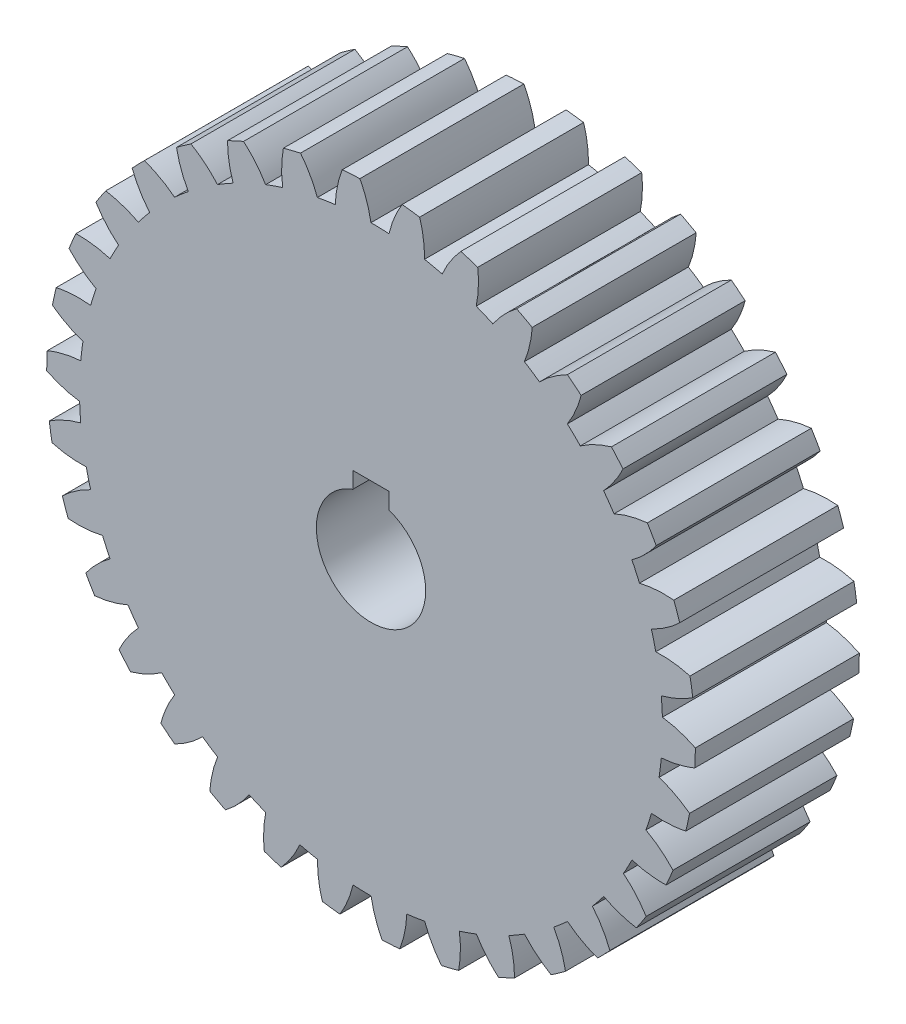
SolidWorks part; units mm, degrees
ref_plane "Front Plane" through (0, 0, 0) normal (0, 0, 1) x (1, 0, 0)
ref_plane "Top Plane" through (0, 0, 0) normal (0, 1, 0) x (1, 0, 0)
ref_plane "Right Plane" through (0, 0, 0) normal (1, 0, 0) x (0, 0, -1)
sketch "Sketch1" plane through (0, 0, 0) normal (0, 0, 1) x (1, 0, 0)
  line L0 (0, 0) -> (0, 31.945) construction
  line L1 (0, 0) -> (-6.9142, 31.1878) construction
  line L2 (0, 0) -> (-13.5005, 28.952) construction
  line L3 (0, 0) -> (-19.4469, 25.3437) construction
  line L4 (0, 0) -> (-24.4713, 20.5339) construction
  line L5 (-6.9142, 31.1878) -> (-0.1094, 32.6964) construction
  line L6 (-13.5005, 28.952) -> (-0.8666, 34.8433) construction
  line L7 (-19.4469, 25.3437) -> (-2.8579, 38.0729) construction
  line L8 (-24.4713, 20.5339) -> (-6.5504, 41.8912) construction
  line L9 (-0.5242, 33.996) -> (-3.6598, 33.8025) construction
  line L10 (-2.092, 33.8992) -> (0, 0) construction
  circle A0 centre (0, 0) radius 31.945 construction
  circle A1 centre (0, 0) radius 34 construction
  arc A2 (-1.2244, 35.5789) -> (-3.1595, 35.4595) centre (0, 0) ccw
  circle A3 centre (0, 0) radius 32
  spline S0 degree 3 poles (-0.0085, 32) (-0.1653, 32.9957) (-0.5453, 34.2042) (-1.0976, 35.3372) (-1.2244, 35.5789) knots 0.004504 0.004504 0.004504 0.004504 0.249371 0.316995 0.316995 0.316995 0.316995
  spline S1 degree 3 poles (-3.9261, 31.7582) (-3.893, 32.7657) (-3.6645, 34.0117) (-3.2557, 35.204) (-3.1595, 35.4595) knots 0.004504 0.004504 0.004504 0.004504 0.249371 0.316995 0.316995 0.316995 0.316995
  point P11 (0, 0)
  dimension "D3" = 63.89
  dimension "D8" = 68
  dimension "D10" = 71.2
  dimension "D11" = 64
  dimension "D2" = 50
  dimension "D4" = 6.97
  dimension "D5" = 13.94
  dimension "D6" = 20.91
  dimension "D7" = 27.88
  dimension "D9" = 3.1416
  dimension "D1" = 5
sketch "Sketch2" plane through (0, 0, 0) normal (0, 0, 1) x (1, 0, 0)
  circle A0 centre (0, 0) radius 32
  dimension "D1" = 64
extrude "Boss-Extrude1" add sketch "Sketch2" along normal blind 18
sketch "Sketch3" plane through (0, 0, 18) normal (0, 0, 1) x (1, 0, 0)
  circle A0 centre (0, 0) radius 32 construction
  arc A1 (-1.2244, 35.5789) -> (-3.1595, 35.4595) centre (0, 0) ccw construction
  arc A2 (-0.0085, 32) -> (-3.9261, 31.7582) centre (0, 0) ccw
  arc A3 (-1.2244, 35.5789) -> (-3.1595, 35.4595) centre (0, 0) ccw
  arc A4 (5.334, 35.1981) -> (3.41, 35.4363) centre (0, 0) ccw
  arc A5 (5.8716, 31.4567) -> (1.9763, 31.9389) centre (0, 0) ccw
  arc A6 (11.7108, 33.6187) -> (9.8633, 34.2064) centre (0, 0) ccw
  arc A7 (11.5518, 29.8422) -> (7.8114, 31.032) centre (0, 0) ccw
  arc A8 (17.6889, 30.8944) -> (15.9808, 31.8115) centre (0, 0) ccw
  arc A9 (16.8386, 27.2114) -> (13.3805, 29.0682) centre (0, 0) ccw
  arc A10 (23.0645, 27.1181) -> (21.554, 28.3334) centre (0, 0) ccw
  arc A11 (21.552, 23.654) -> (18.4939, 26.1146) centre (0, 0) ccw
  arc A12 (27.6547, 22.4182) -> (26.3933, 23.8905) centre (0, 0) ccw
  arc A13 (25.5314, 19.2911) -> (22.9776, 22.2717) centre (0, 0) ccw
  arc A14 (31.3032, 16.955) -> (30.3338, 18.6339) centre (0, 0) ccw
  arc A15 (28.6414, 14.2712) -> (26.6788, 17.6704) centre (0, 0) ccw
  arc A16 (33.8856, 10.9143) -> (33.2412, 12.7428) centre (0, 0) ccw
  arc A17 (30.7761, 8.7654) -> (29.4714, 12.4673) centre (0, 0) ccw
  arc A18 (35.3142, 4.502) -> (35.0167, 6.4178) centre (0, 0) ccw
  arc A19 (31.8627, 2.9611) -> (31.2605, 6.8397) centre (0, 0) ccw
  arc A20 (35.5401, -2.0636) -> (35.5998, -0.1258) centre (0, 0) ccw
  arc A21 (31.8643, -2.9441) -> (31.985, 0.9791) centre (0, 0) ccw
  arc A22 (34.5558, -8.5589) -> (34.9705, -6.6651) centre (0, 0) ccw
  arc A23 (30.7807, -8.749) -> (31.6203, -4.9148) centre (0, 0) ccw
  arc A24 (32.3947, -14.7628) -> (33.1504, -12.9774) centre (0, 0) ccw
  arc A25 (28.649, -14.256) -> (30.1788, -10.6413) centre (0, 0) ccw
  arc A26 (29.1305, -20.464) -> (30.2013, -18.8478) centre (0, 0) ccw
  arc A27 (25.5417, -19.2775) -> (27.7096, -16.0055) centre (0, 0) ccw
  arc A28 (24.8742, -25.4682) -> (26.2238, -24.0764) centre (0, 0) ccw
  arc A29 (21.5645, -23.6426) -> (24.2968, -20.8246) centre (0, 0) ccw
  arc A30 (19.7709, -29.6052) -> (21.3533, -28.485) centre (0, 0) ccw
  arc A31 (16.8531, -27.2025) -> (20.0566, -24.9345) centre (0, 0) ccw
  arc A32 (13.9944, -32.7341) -> (15.7556, -31.9237) centre (0, 0) ccw
  arc A33 (11.5677, -29.836) -> (15.1334, -28.1954) centre (0, 0) ccw
  arc A34 (7.7412, -34.7481) -> (9.6214, -34.2752) centre (0, 0) ccw
  arc A35 (5.8883, -31.4536) -> (9.6949, -30.4961) centre (0, 0) ccw
  arc A36 (1.2244, -35.5789) -> (3.1595, -35.4595) centre (0, 0) ccw
  arc A37 (0.0085, -32) -> (3.9261, -31.7582) centre (0, 0) ccw
  arc A38 (-5.334, -35.1981) -> (-3.41, -35.4363) centre (0, 0) ccw
  arc A39 (-5.8716, -31.4567) -> (-1.9763, -31.9389) centre (0, 0) ccw
  arc A40 (-11.7108, -33.6187) -> (-9.8633, -34.2064) centre (0, 0) ccw
  arc A41 (-11.5518, -29.8422) -> (-7.8114, -31.032) centre (0, 0) ccw
  arc A42 (-17.6889, -30.8944) -> (-15.9808, -31.8115) centre (0, 0) ccw
  arc A43 (-16.8386, -27.2114) -> (-13.3805, -29.0682) centre (0, 0) ccw
  arc A44 (-23.0645, -27.1181) -> (-21.554, -28.3334) centre (0, 0) ccw
  arc A45 (-21.552, -23.654) -> (-18.4939, -26.1146) centre (0, 0) ccw
  arc A46 (-27.6547, -22.4182) -> (-26.3933, -23.8905) centre (0, 0) ccw
  arc A47 (-25.5314, -19.2911) -> (-22.9776, -22.2717) centre (0, 0) ccw
  arc A48 (-31.3032, -16.955) -> (-30.3338, -18.6339) centre (0, 0) ccw
  arc A49 (-28.6414, -14.2712) -> (-26.6788, -17.6704) centre (0, 0) ccw
  arc A50 (-33.8856, -10.9143) -> (-33.2412, -12.7428) centre (0, 0) ccw
  arc A51 (-30.7761, -8.7654) -> (-29.4714, -12.4673) centre (0, 0) ccw
  arc A52 (-35.3142, -4.502) -> (-35.0167, -6.4178) centre (0, 0) ccw
  arc A53 (-31.8627, -2.9611) -> (-31.2605, -6.8397) centre (0, 0) ccw
  arc A54 (-35.5401, 2.0636) -> (-35.5998, 0.1258) centre (0, 0) ccw
  arc A55 (-31.8643, 2.9441) -> (-31.985, -0.9791) centre (0, 0) ccw
  arc A56 (-34.5558, 8.5589) -> (-34.9705, 6.6651) centre (0, 0) ccw
  arc A57 (-30.7807, 8.749) -> (-31.6203, 4.9148) centre (0, 0) ccw
  arc A58 (-32.3947, 14.7628) -> (-33.1504, 12.9774) centre (0, 0) ccw
  arc A59 (-28.649, 14.256) -> (-30.1788, 10.6413) centre (0, 0) ccw
  arc A60 (-29.1305, 20.464) -> (-30.2013, 18.8478) centre (0, 0) ccw
  arc A61 (-25.5417, 19.2775) -> (-27.7096, 16.0055) centre (0, 0) ccw
  arc A62 (-24.8742, 25.4682) -> (-26.2238, 24.0764) centre (0, 0) ccw
  arc A63 (-21.5645, 23.6426) -> (-24.2968, 20.8246) centre (0, 0) ccw
  arc A64 (-19.7709, 29.6052) -> (-21.3533, 28.485) centre (0, 0) ccw
  arc A65 (-16.8531, 27.2025) -> (-20.0566, 24.9345) centre (0, 0) ccw
  arc A66 (-13.9944, 32.7341) -> (-15.7556, 31.9237) centre (0, 0) ccw
  arc A67 (-11.5677, 29.836) -> (-15.1334, 28.1954) centre (0, 0) ccw
  arc A68 (-7.7412, 34.7481) -> (-9.6214, 34.2752) centre (0, 0) ccw
  arc A69 (-5.8883, 31.4536) -> (-9.6949, 30.4961) centre (0, 0) ccw
  spline S0 degree 3 poles (-2952.0058, -485.1321) (-147.5375, -118.176) (204.0978, 131.3339) (-278.5397, 15.7851) (2997.7022, 113.4453) knots -9.84774 -9.84774 -9.84774 -9.84774 0.249371 11.892847 11.892847 11.892847 11.892847 only from (-0.0085, 32) to (-1.2244, 35.5789) construction
  spline S1 degree 3 poles (2989.2564, -118.4971) (160.9487, -99.1389) (-218.6978, 105.2425) (274.4857, 49.9132) (-2988.9027, -255.9828) knots -9.847748 -9.847748 -9.847748 -9.847748 0.249371 11.892857 11.892857 11.892857 11.892857 only from (-3.9261, 31.7582) to (-3.1595, 35.4595) construction
  spline S2 degree 3 poles (-0.0085, 32) (-0.1653, 32.9957) (-0.5453, 34.2042) (-1.0976, 35.3372) (-1.2244, 35.5789) knots 0.004504 0.004504 0.004504 0.004504 0.249371 0.316995 0.316995 0.316995 0.316995
  spline S3 degree 3 poles (-3.9261, 31.7582) (-3.893, 32.7657) (-3.6645, 34.0117) (-3.2557, 35.204) (-3.1595, 35.4595) knots 0.004504 0.004504 0.004504 0.004504 0.249371 0.316995 0.316995 0.316995 0.316995
  spline S4 degree 3 poles (1.9763, 31.9389) (2.194, 32.9231) (2.6475, 34.1059) (3.2685, 35.2029) (3.41, 35.4363) knots 0.004504 0.004504 0.004504 0.004504 0.249371 0.316995 0.316995 0.316995 0.316995
  spline S5 degree 3 poles (5.8716, 31.4567) (5.9005, 32.4643) (5.749, 33.722) (5.4143, 34.9372) (5.334, 35.1981) knots 0.004504 0.004504 0.004504 0.004504 0.249371 0.316995 0.316995 0.316995 0.316995
  spline S6 degree 3 poles (7.8114, 31.032) (8.2062, 31.9594) (8.8694, 33.0387) (9.6814, 34.0029) (9.8633, 34.2064) knots 0.004504 0.004504 0.004504 0.004504 0.249371 0.316995 0.316995 0.316995 0.316995
  spline S7 degree 3 poles (11.5518, 29.8422) (11.7653, 30.8273) (11.8475, 32.0914) (11.7418, 33.3475) (11.7108, 33.6187) knots 0.004504 0.004504 0.004504 0.004504 0.249371 0.316995 0.316995 0.316995 0.316995
  spline S8 degree 3 poles (13.3805, 29.0682) (13.939, 29.9073) (14.7892, 30.8464) (15.7645, 31.645) (15.9808, 31.8115) knots 0.004504 0.004504 0.004504 0.004504 0.249371 0.316995 0.316995 0.316995 0.316995
  spline S9 degree 3 poles (16.8386, 27.2114) (17.2295, 28.1405) (17.5426, 29.368) (17.6695, 30.6221) (17.6889, 30.8944) knots 0.004504 0.004504 0.004504 0.004504 0.249371 0.316995 0.316995 0.316995 0.316995
  spline S10 degree 3 poles (18.4939, 26.1146) (19.1972, 26.8368) (20.2054, 27.6037) (21.3108, 28.2094) (21.554, 28.3334) knots 0.004504 0.004504 0.004504 0.004504 0.249371 0.316995 0.316995 0.316995 0.316995
  spline S11 degree 3 poles (21.552, 23.654) (22.1069, 24.4955) (22.6403, 25.6445) (22.9954, 26.854) (23.0645, 27.1181) knots 0.004504 0.004504 0.004504 0.004504 0.249371 0.316995 0.316995 0.316995 0.316995
  spline S12 degree 3 poles (22.9776, 22.2717) (23.8015, 22.8524) (24.9336, 23.4209) (26.1315, 23.8132) (26.3933, 23.8905) knots 0.004504 0.004504 0.004504 0.004504 0.249371 0.316995 0.316995 0.316995 0.316995
  spline S13 degree 3 poles (25.5314, 19.2911) (26.2315, 20.0163) (26.9669, 21.0478) (27.5383, 22.1713) (27.6547, 22.4182) knots 0.004504 0.004504 0.004504 0.004504 0.249371 0.316995 0.316995 0.316995 0.316995
  spline S14 degree 3 poles (26.6788, 17.6704) (27.5954, 18.0898) (28.8126, 18.4406) (30.0622, 18.6061) (30.3338, 18.6339) knots 0.004504 0.004504 0.004504 0.004504 0.249371 0.316995 0.316995 0.316995 0.316995
  spline S15 degree 3 poles (28.6414, 14.2712) (29.4629, 14.8554) (30.3753, 15.7342) (31.1433, 16.7337) (31.3032, 16.955) knots 0.004504 0.004504 0.004504 0.004504 0.249371 0.316995 0.316995 0.316995 0.316995
  spline S16 degree 3 poles (29.4714, 12.4673) (30.4495, 12.7111) (31.7105, 12.8323) (32.9692, 12.7654) (33.2412, 12.7428) knots 0.004504 0.004504 0.004504 0.004504 0.249371 0.316995 0.316995 0.316995 0.316995
  spline S17 degree 3 poles (30.7761, 8.7654) (31.6909, 9.1887) (32.7492, 9.8849) (33.6879, 10.7262) (33.8856, 10.9143) knots 0.004504 0.004504 0.004504 0.004504 0.249371 0.316995 0.316995 0.316995 0.316995
  spline S18 degree 3 poles (31.2605, 6.8397) (32.2667, 6.8996) (33.5285, 6.787) (34.7535, 6.49) (35.0167, 6.4178) knots 0.004504 0.004504 0.004504 0.004504 0.249371 0.316995 0.316995 0.316995 0.316995
  spline S19 degree 3 poles (31.8627, 2.9611) (32.8397, 3.2091) (34.008, 3.6989) (35.0852, 4.3534) (35.3142, 4.502) knots 0.004504 0.004504 0.004504 0.004504 0.249371 0.316995 0.316995 0.316995 0.316995
  spline S20 degree 3 poles (31.985, 0.9791) (32.9851, 0.8531) (34.2047, 0.5106) (35.3543, -0.0064) (35.5998, -0.1258) knots 0.004504 0.004504 0.004504 0.004504 0.249371 0.316995 0.316995 0.316995 0.316995
  spline S21 degree 3 poles (31.8643, -2.9441) (32.8702, -2.8799) (34.1086, -2.613) (35.2878, -2.1676) (35.5401, -2.0636) knots 0.004504 0.004504 0.004504 0.004504 0.249371 0.316995 0.316995 0.316995 0.316995
  spline S22 degree 3 poles (31.6203, -4.9148) (32.5802, -5.2224) (33.7161, -5.7832) (34.7511, -6.5027) (34.9705, -6.6651) knots 0.004504 0.004504 0.004504 0.004504 0.249371 0.316995 0.316995 0.316995 0.316995
  spline S23 degree 3 poles (30.7807, -8.749) (31.7814, -8.8707) (33.0477, -8.836) (34.2886, -8.6148) (34.5558, -8.5589) knots 0.004504 0.004504 0.004504 0.004504 0.249371 0.316995 0.316995 0.316995 0.316995
  spline S24 degree 3 poles (30.1788, -10.6413) (31.0659, -11.1201) (32.0794, -11.88) (32.9645, -12.7774) (33.1504, -12.9774) knots 0.004504 0.004504 0.004504 0.004504 0.249371 0.316995 0.316995 0.316995 0.316995
  spline S25 degree 3 poles (28.649, -14.256) (29.6102, -14.5595) (30.8614, -14.758) (32.1218, -14.7686) (32.3947, -14.7628) knots 0.004504 0.004504 0.004504 0.004504 0.249371 0.316995 0.316995 0.316995 0.316995
  spline S26 degree 3 poles (27.7096, -16.0055) (28.4936, -16.6391) (29.3503, -17.5723) (30.0554, -18.6171) (30.2013, -18.8478) knots 0.004504 0.004504 0.004504 0.004504 0.249371 0.316995 0.316995 0.316995 0.316995
  spline S27 degree 3 poles (25.5417, -19.2775) (26.4308, -19.7524) (27.6241, -20.1775) (28.8612, -20.4195) (29.1305, -20.464) knots 0.004504 0.004504 0.004504 0.004504 0.249371 0.316995 0.316995 0.316995 0.316995
  spline S28 degree 3 poles (24.2968, -20.8246) (24.951, -21.5915) (25.6216, -22.6662) (26.1228, -23.8228) (26.2238, -24.0764) knots 0.004504 0.004504 0.004504 0.004504 0.249371 0.316995 0.316995 0.316995 0.316995
  spline S29 degree 3 poles (21.5645, -23.6426) (22.3512, -24.2728) (23.4462, -24.9099) (24.6177, -25.3751) (24.8742, -25.4682) knots 0.004504 0.004504 0.004504 0.004504 0.249371 0.316995 0.316995 0.316995 0.316995
  spline S30 degree 3 poles (20.0566, -24.9345) (20.5588, -25.8086) (21.0204, -26.9882) (21.3006, -28.2172) (21.3533, -28.485) knots 0.004504 0.004504 0.004504 0.004504 0.249371 0.316995 0.316995 0.316995 0.316995
  spline S31 degree 3 poles (16.8531, -27.2025) (17.5106, -27.9665) (18.4698, -28.7939) (19.5358, -29.4665) (19.7709, -29.6052) knots 0.004504 0.004504 0.004504 0.004504 0.249371 0.316995 0.316995 0.316995 0.316995
  spline S32 degree 3 poles (15.1334, -28.1954) (15.4664, -29.1468) (15.7035, -30.3912) (15.753, -31.6507) (15.7556, -31.9237) knots 0.004504 0.004504 0.004504 0.004504 0.249371 0.316995 0.316995 0.316995 0.316995
  spline S33 degree 3 poles (11.5677, -29.836) (12.0736, -30.7079) (12.8644, -31.6975) (13.7887, -32.5545) (13.9944, -32.7341) knots 0.004504 0.004504 0.004504 0.004504 0.249371 0.316995 0.316995 0.316995 0.316995
  spline S34 degree 3 poles (9.6949, -30.4961) (9.8474, -31.4924) (9.8517, -32.7592) (9.669, -34.0064) (9.6214, -34.2752) knots 0.004504 0.004504 0.004504 0.004504 0.249371 0.316995 0.316995 0.316995 0.316995
  spline S35 degree 3 poles (5.8883, -31.4536) (6.2254, -32.4035) (6.821, -33.5216) (7.5721, -34.5339) (7.7412, -34.7481) knots 0.004504 0.004504 0.004504 0.004504 0.249371 0.316995 0.316995 0.316995 0.316995
  spline S36 degree 3 poles (3.9261, -31.7582) (3.893, -32.7657) (3.6645, -34.0117) (3.2557, -35.204) (3.1595, -35.4595) knots 0.004504 0.004504 0.004504 0.004504 0.249371 0.316995 0.316995 0.316995 0.316995
  spline S37 degree 3 poles (0.0085, -32) (0.1653, -32.9957) (0.5453, -34.2042) (1.0976, -35.3372) (1.2244, -35.5789) knots 0.004504 0.004504 0.004504 0.004504 0.249371 0.316995 0.316995 0.316995 0.316995
  spline S38 degree 3 poles (-1.9763, -31.9389) (-2.194, -32.9231) (-2.6475, -34.1059) (-3.2685, -35.2029) (-3.41, -35.4363) knots 0.004504 0.004504 0.004504 0.004504 0.249371 0.316995 0.316995 0.316995 0.316995
  spline S39 degree 3 poles (-5.8716, -31.4567) (-5.9005, -32.4643) (-5.749, -33.722) (-5.4143, -34.9372) (-5.334, -35.1981) knots 0.004504 0.004504 0.004504 0.004504 0.249371 0.316995 0.316995 0.316995 0.316995
  spline S40 degree 3 poles (-7.8114, -31.032) (-8.2062, -31.9594) (-8.8694, -33.0387) (-9.6814, -34.0029) (-9.8633, -34.2064) knots 0.004504 0.004504 0.004504 0.004504 0.249371 0.316995 0.316995 0.316995 0.316995
  spline S41 degree 3 poles (-11.5518, -29.8422) (-11.7653, -30.8273) (-11.8475, -32.0914) (-11.7418, -33.3475) (-11.7108, -33.6187) knots 0.004504 0.004504 0.004504 0.004504 0.249371 0.316995 0.316995 0.316995 0.316995
  spline S42 degree 3 poles (-13.3805, -29.0682) (-13.939, -29.9073) (-14.7892, -30.8464) (-15.7645, -31.645) (-15.9808, -31.8115) knots 0.004504 0.004504 0.004504 0.004504 0.249371 0.316995 0.316995 0.316995 0.316995
  spline S43 degree 3 poles (-16.8386, -27.2114) (-17.2295, -28.1405) (-17.5426, -29.368) (-17.6695, -30.6221) (-17.6889, -30.8944) knots 0.004504 0.004504 0.004504 0.004504 0.249371 0.316995 0.316995 0.316995 0.316995
  spline S44 degree 3 poles (-18.4939, -26.1146) (-19.1972, -26.8368) (-20.2054, -27.6037) (-21.3108, -28.2094) (-21.554, -28.3334) knots 0.004504 0.004504 0.004504 0.004504 0.249371 0.316995 0.316995 0.316995 0.316995
  spline S45 degree 3 poles (-21.552, -23.654) (-22.1069, -24.4955) (-22.6403, -25.6445) (-22.9954, -26.854) (-23.0645, -27.1181) knots 0.004504 0.004504 0.004504 0.004504 0.249371 0.316995 0.316995 0.316995 0.316995
  spline S46 degree 3 poles (-22.9776, -22.2717) (-23.8015, -22.8524) (-24.9336, -23.4209) (-26.1315, -23.8132) (-26.3933, -23.8905) knots 0.004504 0.004504 0.004504 0.004504 0.249371 0.316995 0.316995 0.316995 0.316995
  spline S47 degree 3 poles (-25.5314, -19.2911) (-26.2315, -20.0163) (-26.9669, -21.0478) (-27.5383, -22.1713) (-27.6547, -22.4182) knots 0.004504 0.004504 0.004504 0.004504 0.249371 0.316995 0.316995 0.316995 0.316995
  spline S48 degree 3 poles (-26.6788, -17.6704) (-27.5954, -18.0898) (-28.8126, -18.4406) (-30.0622, -18.6061) (-30.3338, -18.6339) knots 0.004504 0.004504 0.004504 0.004504 0.249371 0.316995 0.316995 0.316995 0.316995
  spline S49 degree 3 poles (-28.6414, -14.2712) (-29.4629, -14.8554) (-30.3753, -15.7342) (-31.1433, -16.7337) (-31.3032, -16.955) knots 0.004504 0.004504 0.004504 0.004504 0.249371 0.316995 0.316995 0.316995 0.316995
  spline S50 degree 3 poles (-29.4714, -12.4673) (-30.4495, -12.7111) (-31.7105, -12.8323) (-32.9692, -12.7654) (-33.2412, -12.7428) knots 0.004504 0.004504 0.004504 0.004504 0.249371 0.316995 0.316995 0.316995 0.316995
  spline S51 degree 3 poles (-30.7761, -8.7654) (-31.6909, -9.1887) (-32.7492, -9.8849) (-33.6879, -10.7262) (-33.8856, -10.9143) knots 0.004504 0.004504 0.004504 0.004504 0.249371 0.316995 0.316995 0.316995 0.316995
  spline S52 degree 3 poles (-31.2605, -6.8397) (-32.2667, -6.8996) (-33.5285, -6.787) (-34.7535, -6.49) (-35.0167, -6.4178) knots 0.004504 0.004504 0.004504 0.004504 0.249371 0.316995 0.316995 0.316995 0.316995
  spline S53 degree 3 poles (-31.8627, -2.9611) (-32.8397, -3.2091) (-34.008, -3.6989) (-35.0852, -4.3534) (-35.3142, -4.502) knots 0.004504 0.004504 0.004504 0.004504 0.249371 0.316995 0.316995 0.316995 0.316995
  spline S54 degree 3 poles (-31.985, -0.9791) (-32.9851, -0.8531) (-34.2047, -0.5106) (-35.3543, 0.0064) (-35.5998, 0.1258) knots 0.004504 0.004504 0.004504 0.004504 0.249371 0.316995 0.316995 0.316995 0.316995
  spline S55 degree 3 poles (-31.8643, 2.9441) (-32.8702, 2.8799) (-34.1086, 2.613) (-35.2878, 2.1676) (-35.5401, 2.0636) knots 0.004504 0.004504 0.004504 0.004504 0.249371 0.316995 0.316995 0.316995 0.316995
  spline S56 degree 3 poles (-31.6203, 4.9148) (-32.5802, 5.2224) (-33.7161, 5.7832) (-34.7511, 6.5027) (-34.9705, 6.6651) knots 0.004504 0.004504 0.004504 0.004504 0.249371 0.316995 0.316995 0.316995 0.316995
  spline S57 degree 3 poles (-30.7807, 8.749) (-31.7814, 8.8707) (-33.0477, 8.836) (-34.2886, 8.6148) (-34.5558, 8.5589) knots 0.004504 0.004504 0.004504 0.004504 0.249371 0.316995 0.316995 0.316995 0.316995
  spline S58 degree 3 poles (-30.1788, 10.6413) (-31.0659, 11.1201) (-32.0794, 11.88) (-32.9645, 12.7774) (-33.1504, 12.9774) knots 0.004504 0.004504 0.004504 0.004504 0.249371 0.316995 0.316995 0.316995 0.316995
  spline S59 degree 3 poles (-28.649, 14.256) (-29.6102, 14.5595) (-30.8614, 14.758) (-32.1218, 14.7686) (-32.3947, 14.7628) knots 0.004504 0.004504 0.004504 0.004504 0.249371 0.316995 0.316995 0.316995 0.316995
  spline S60 degree 3 poles (-27.7096, 16.0055) (-28.4936, 16.6391) (-29.3503, 17.5723) (-30.0554, 18.6171) (-30.2013, 18.8478) knots 0.004504 0.004504 0.004504 0.004504 0.249371 0.316995 0.316995 0.316995 0.316995
  spline S61 degree 3 poles (-25.5417, 19.2775) (-26.4308, 19.7524) (-27.6241, 20.1775) (-28.8612, 20.4195) (-29.1305, 20.464) knots 0.004504 0.004504 0.004504 0.004504 0.249371 0.316995 0.316995 0.316995 0.316995
  spline S62 degree 3 poles (-24.2968, 20.8246) (-24.951, 21.5915) (-25.6216, 22.6662) (-26.1228, 23.8228) (-26.2238, 24.0764) knots 0.004504 0.004504 0.004504 0.004504 0.249371 0.316995 0.316995 0.316995 0.316995
  spline S63 degree 3 poles (-21.5645, 23.6426) (-22.3512, 24.2728) (-23.4462, 24.9099) (-24.6177, 25.3751) (-24.8742, 25.4682) knots 0.004504 0.004504 0.004504 0.004504 0.249371 0.316995 0.316995 0.316995 0.316995
  spline S64 degree 3 poles (-20.0566, 24.9345) (-20.5588, 25.8086) (-21.0204, 26.9882) (-21.3006, 28.2172) (-21.3533, 28.485) knots 0.004504 0.004504 0.004504 0.004504 0.249371 0.316995 0.316995 0.316995 0.316995
  spline S65 degree 3 poles (-16.8531, 27.2025) (-17.5106, 27.9665) (-18.4698, 28.7939) (-19.5358, 29.4665) (-19.7709, 29.6052) knots 0.004504 0.004504 0.004504 0.004504 0.249371 0.316995 0.316995 0.316995 0.316995
  spline S66 degree 3 poles (-15.1334, 28.1954) (-15.4664, 29.1468) (-15.7035, 30.3912) (-15.753, 31.6507) (-15.7556, 31.9237) knots 0.004504 0.004504 0.004504 0.004504 0.249371 0.316995 0.316995 0.316995 0.316995
  spline S67 degree 3 poles (-11.5677, 29.836) (-12.0736, 30.7079) (-12.8644, 31.6975) (-13.7887, 32.5545) (-13.9944, 32.7341) knots 0.004504 0.004504 0.004504 0.004504 0.249371 0.316995 0.316995 0.316995 0.316995
  spline S68 degree 3 poles (-9.6949, 30.4961) (-9.8474, 31.4924) (-9.8517, 32.7592) (-9.669, 34.0064) (-9.6214, 34.2752) knots 0.004504 0.004504 0.004504 0.004504 0.249371 0.316995 0.316995 0.316995 0.316995
  spline S69 degree 3 poles (-5.8883, 31.4536) (-6.2254, 32.4035) (-6.821, 33.5216) (-7.5721, 34.5339) (-7.7412, 34.7481) knots 0.004504 0.004504 0.004504 0.004504 0.249371 0.316995 0.316995 0.316995 0.316995
  point P141 (0, 0)
  dimension "D1" = 34
extrude "Boss-Extrude2" add sketch "Sketch3" against normal through all
sketch "Sketch4" plane through (0, 0, 18) normal (0, 0, 1) x (1, 0, 0)
  circle A0 centre (0, 0) radius 6
  dimension "D1" = 12
extrude "Cut-Extrude1" cut sketch "Sketch4" against normal through all
sketch "Sketch5" plane through (0, 0, 18) normal (0, 0, 1) x (1, 0, 0)
  line L0 (0, 0) -> (0, 6) construction
  line L1 (-2, 5.6569) -> (2, 5.6569)
  line L2 (-2, 5.6569) -> (-2, 7.4569)
  line L3 (-2, 7.4569) -> (2, 7.4569)
  line L4 (2, 5.6569) -> (2, 7.4569)
  circle A0 centre (0, 0) radius 6 construction
  dimension "D1" = 1.8
  dimension "D2" = 4
extrude "Cut-Extrude2" cut sketch "Sketch5" against normal blind 8
